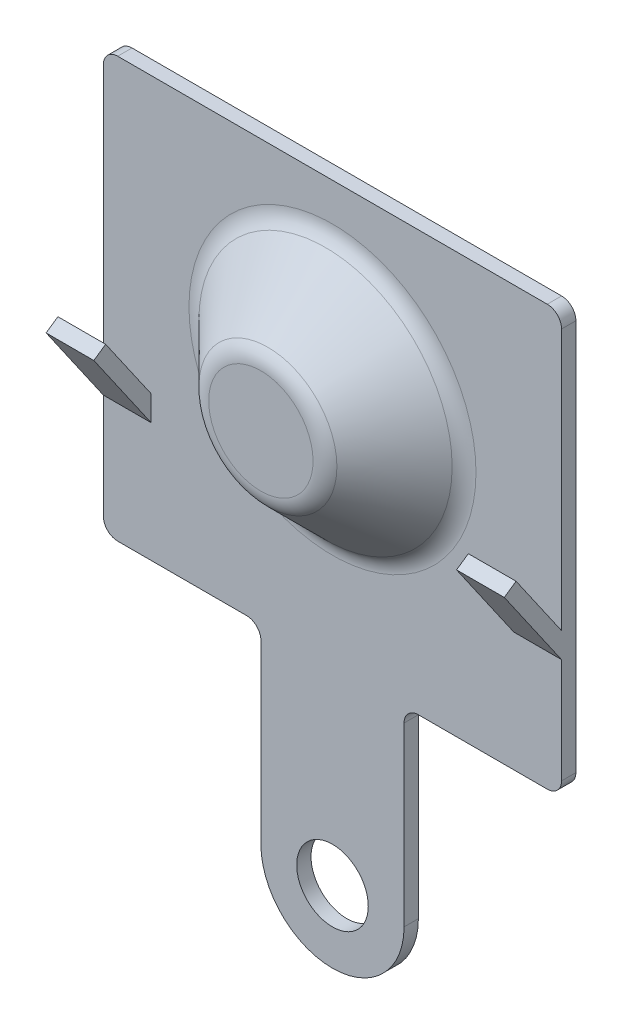
SolidWorks part; units mm, degrees
ref_plane "Front Plane" through (0, 0, 0) normal (0, 0, 1) x (1, 0, 0)
ref_plane "Top Plane" through (0, 0, 0) normal (0, 1, 0) x (1, 0, 0)
ref_plane "Right Plane" through (0, 0, 0) normal (1, 0, 0) x (0, 0, -1)
sketch "Sketch1" plane through (0, 0, 0) normal (0, 0, 1) x (1, 0, 0)
  line L0 (0, 0) -> (0, 4.4) construction
  line L1 (-4.8, 4.4) -> (4.8, 4.4)
  line L2 (4.8, 4.4) -> (4.8, -4.4)
  line L3 (4.8, -4.4) -> (1.5, -4.4)
  line L4 (1.5, -4.4) -> (1.5, -8.4)
  line L5 (0, 0) -> (0, -8.4) construction
  line L6 (-1.5, -4.4) -> (-1.5, -8.4)
  line L7 (-4.8, -4.4) -> (-1.5, -4.4)
  line L8 (-4.8, 4.4) -> (-4.8, -4.4)
  line L9 (-2.6852, -9.9) -> (3.5735, -9.9) construction
  line L10 (0, 0) -> (4.8, 0) construction
  arc A0 (1.5, -8.4) -> (-1.5, -8.4) centre (0, -8.4) cw
  circle A1 centre (0, -8.4) radius 0.75
  dimension "D5" = 1.5
  dimension "D1" = 9.6
  dimension "D2" = 8.8
  dimension "D3" = 14.3
  dimension "D4" = 3
  dimension "D6" = 9.9
extrude "Boss-Extrude1" add sketch "Sketch1" along normal blind 0.3
fillet "Fillet1" radius 0.3 6 edges at (-1.5, -4.4, 0.15) (1.5, -4.4, 0.15) (4.8, -4.4, 0.15) (-4.8, -4.4, 0.15) (-4.8, 4.4, 0.15) (4.8, 4.4, 0.15)
sketch "Sketch2" plane through (4.8, 0, 0) normal (1, 0, 0) x (0, 0, -1)
  line L0 (-0.3, -1.9) -> (-1.5, -0.1711)
  line L1 (-0.3, -4.1) -> (-0.3, 4.1) construction
  line L2 (-1.5, -0.1711) -> (-1.2535, 0)
  line L3 (-1.2535, 0) -> (-0.3, -1.3739)
  line L4 (-0.3, -1.3739) -> (-0.3, -1.9)
  line L5 (-0.3, 4.4) -> (0, 4.4) construction
  line L6 (0, -4.1) -> (0, 4.1) construction
  line L7 (0, -4.4) -> (-0.3, -4.4) construction
  dimension "D1" = 0.3
  dimension "D2" = 6.3
  dimension "D3" = 1.5
  dimension "D4" = 4.4
extrude "Boss-Extrude2" add sketch "Sketch2" against normal blind 1
mirror "Mirror1" about plane through (0, 0, 0) normal (1, 0, 0) of "Boss-Extrude2"
sketch "Sketch3" plane through (0, 0, 0) normal (1, 0, 0) x (0, 0, -1)
  line L0 (-1.8, 0.6) -> (-1.8, 1.9)
  line L1 (-1.8, 1.9) -> (-0.3, 3.4)
  line L2 (-0.3, 3.4) -> (-0.3, 0.6)
  line L3 (-0.3, 0.6) -> (-1.8, 0.6)
  line L4 (-0.3, -1.3739) -> (-0.3, 4.1) construction
  line L5 (0, -4.1) -> (0, 4.1) construction
  line L6 (-0.3, 4.4) -> (0, 4.4) construction
  dimension "D1" = 1.3
  dimension "D2" = 2.8
  dimension "D3" = 1.8
  dimension "D4" = 3.8
revolve "Revolve1" add sketch "Sketch3" angle 360 about L3
fillet "Fillet2" radius 0.5 2 edges at (0, 3.4, 0.3) (0, 1.9, 1.8)
